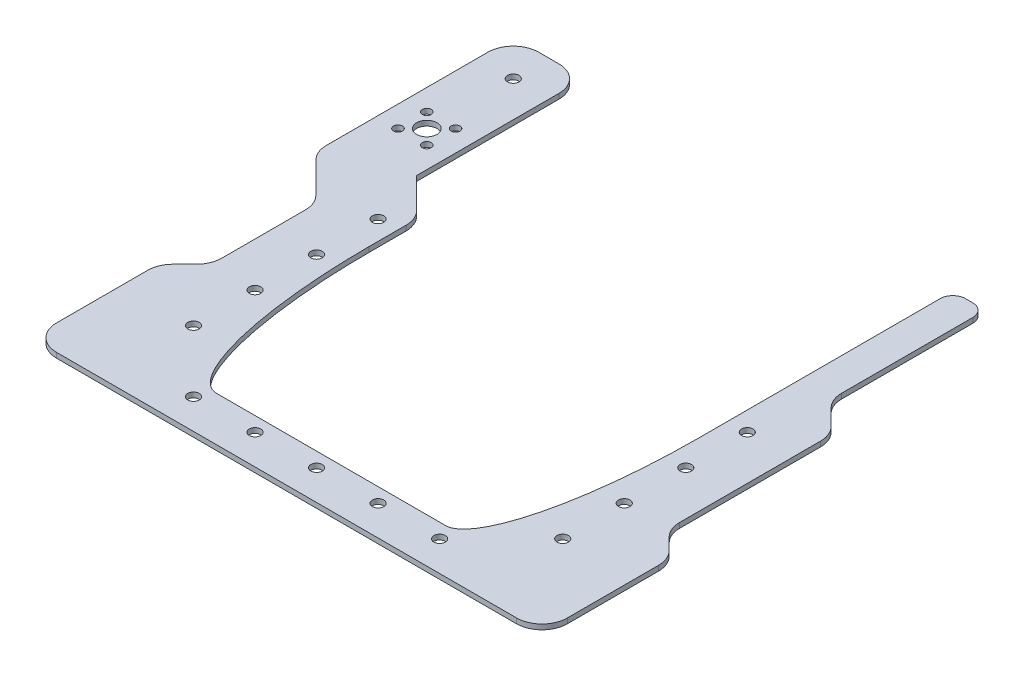
SolidWorks part; units mm, degrees
material "6061-T6 (SS)"
ref_plane "Front Plane" through (0, 0, 0) normal (0, 0, 1) x (1, 0, 0)
ref_plane "Top Plane" through (0, 0, 0) normal (0, 1, 0) x (1, 0, 0)
ref_plane "Right Plane" through (0, 0, 0) normal (1, 0, 0) x (0, 0, -1)
sketch "Sketch1" plane through (0, 0, 0) normal (0, 1, 0) x (1, 0, 0)
  line L0 (0, 0) -> (0, -98.655)
  line L1 (0, -98.655) -> (130, -98.655)
  line L2 (130, -98.655) -> (130, 80.835)
  line L4 (142.835, 80.835) -> (142.835, 20.135)
  line L5 (142.835, 20.135) -> (155, 7.97)
  line L6 (155, 7.97) -> (155, -55.71)
  line L7 (155, -55.71) -> (165.445, -66.155)
  line L8 (165.445, -66.155) -> (165.445, -116.155)
  line L9 (165.445, -116.155) -> (-35.445, -116.155)
  line L10 (-35.445, -116.155) -> (-35.445, -66.155)
  line L11 (-35.445, -66.155) -> (-25, -55.71)
  line L12 (-25, -55.71) -> (-25, -14.598)
  line L13 (-25, -14.598) -> (-42.835, 3.237)
  line L14 (-42.835, 3.237) -> (-42.835, 80.835)
  line L15 (-42.835, 80.835) -> (-14.835, 80.835)
  line L16 (-14.835, 80.835) -> (-14.835, 14.835)
  line L17 (-14.835, 14.835) -> (0, 0)
  line L18 (65, -98.655) -> (65, -116.155) construction
  line L19 (-42.835, 16.835) -> (-14.835, 16.835) construction
  line L20 (-975.5135, 32.835) -> (49024.4865, 32.835) construction
  line L21 (-25, -35.154) -> (155, -35.154) construction
  line L22 (-25, -14.598) -> (-5.201, 5.201) construction
  line L24 (130, 80.835) -> (142.835, 80.835)
  line L27 (142.835, 20.135) -> (117.835, 20.135) construction
  point P27 (65, -35.154)
  dimension "D1" = 200.89
  dimension "D2" = 50
  dimension "D3" = 130
  dimension "D4" = 17.5
  dimension "D5" = 148.99
  dimension "D6" = 16
  dimension "D7" = 7.39
  dimension "D8" = 28
  dimension "D9" = 135
  dimension "D10" = 180
  dimension "D11" = 2
  dimension "D12" = 135
  dimension "D13" = 22.61
  dimension "D14" = 135
  dimension "D15" = 12.7
  dimension "D18" = 48
extrude "Boss-Extrude1" add sketch "Sketch1" along normal blind 2
sketch "Sketch2" plane through (0, 2, 0) normal (0, 1, 0) x (1, 0, 0)
  line L0 (-200975.5135, 32.835) -> (249024.4865, 32.835) construction
  line L1 (-14.835, 80.835) -> (-14.835, 14.835) construction
  line L2 (-28.835, 32.835) -> (-23.1781, 38.4919) construction
  line L3 (65, -98.655) -> (65, -116.155) construction
  line L4 (165.445, -116.155) -> (-35.445, -116.155) construction
  line L5 (65, -116.155) -> (65, -98.655) construction
  line L6 (0, -98.655) -> (130, -98.655) construction
  circle A0 centre (-23.1781, 38.4919) radius 1.75
  circle A1 centre (-23.1781, 27.1781) radius 1.75
  circle A2 centre (-34.4919, 27.1781) radius 1.75
  circle A3 centre (-34.4919, 38.4919) radius 1.75
  circle A4 centre (-28.835, 32.835) radius 4
  circle A5 centre (137.585, -80.14) radius 2.25
  circle A7 centre (-7.585, -80.14) radius 2.25
  circle A8 centre (137.585, -55.945) radius 2.25
  circle A9 centre (-7.585, -55.945) radius 2.25
  circle A10 centre (137.585, -31.75) radius 2.25
  circle A11 centre (-7.585, -31.75) radius 2.25
  circle A12 centre (137.585, -7.555) radius 2.25
  circle A13 centre (-7.585, -7.555) radius 2.25
  circle A15 centre (16.61, -104.335) radius 2.25
  circle A17 centre (40.805, -104.335) radius 2.25
  circle A19 centre (65, -104.335) radius 2.25
  circle A20 centre (89.195, -104.335) radius 2.25
  circle A21 centre (113.39, -104.335) radius 2.25
  point P0 (-28.835, 32.835)
  point P17 (-28.835, 32.835)
  dimension "D3" = 3.5
  dimension "D6" = 8
  dimension "D9" = 4.5
  dimension "D12" = 4.5
  dimension "D1" = 14
  dimension "D2" = 45
  dimension "D4" = 8
  dimension "D7" = 72.585
  dimension "D8" = 36.015
  dimension "D11" = 11.82
  dimension "D10" = 4
  dimension "D5" = 4
extrude "Cut-Extrude2" cut sketch "Sketch2" against normal through all
fillet "Fillet1" radius 10 13 edges at (0, 1, 0) (-42.835, 1, -3.237) (-25, 1, 14.598) (-25, 1, 55.71) (-35.445, 1, 66.155) (155, 1, 55.71) (165.445, 1, 66.155) (165.445, 1, 116.155) (-35.445, 1, 116.155) (-14.835, 1, -80.835) (-42.835, 1, -80.835) (142.835, 1, -20.135) (155, 1, -7.97)
sketch "Sketch3" plane through (0, 2, 0) normal (0, 1, 0) x (1, 0, 0)
  line L0 (130, -98.655) -> (0, -98.655) construction
  line L1 (0, -98.655) -> (0, -4.1421) construction
  line L2 (0, -18.655) -> (0, -98.655)
  line L3 (0, -98.655) -> (20, -98.655)
  line L4 (65, -116.155) -> (65, -98.655) construction
  line L5 (-25.445, -116.155) -> (155.445, -116.155) construction
  line L6 (130, -98.655) -> (110, -98.655)
  line L7 (130, -18.655) -> (130, -98.655)
  ellipse E0 centre (20, -18.655) end of major axis (20, -98.655) minor radius 20 (0, -18.655) -> (20, -98.655) ccw
  ellipse E1 centre (110, -18.655) end of major axis (110, -98.655) minor radius 20 (130, -18.655) -> (110, -98.655) cw
  dimension "D1" = 20
  dimension "D2" = 80
extrude "Boss-Extrude3" add sketch "Sketch3" against normal through all
fillet "Fillet3" radius 5 2 edges at (142.835, 1, -80.835) (130, 1, -80.835)
sketch "Sketch4" plane through (0, 2, 0) normal (0, 1, 0) x (1, 0, 0)
  line L0 (-24.835, 80.835) -> (-32.835, 80.835) construction
  line L1 (-14.835, 14.835) -> (-14.835, 70.835) construction
  circle A0 centre (-28.835, 66.835) radius 2.25
  dimension "D2" = 4.5
  dimension "D1" = 14
  dimension "D3" = 14
extrude "Cut-Extrude3" cut sketch "Sketch4" against normal through all
